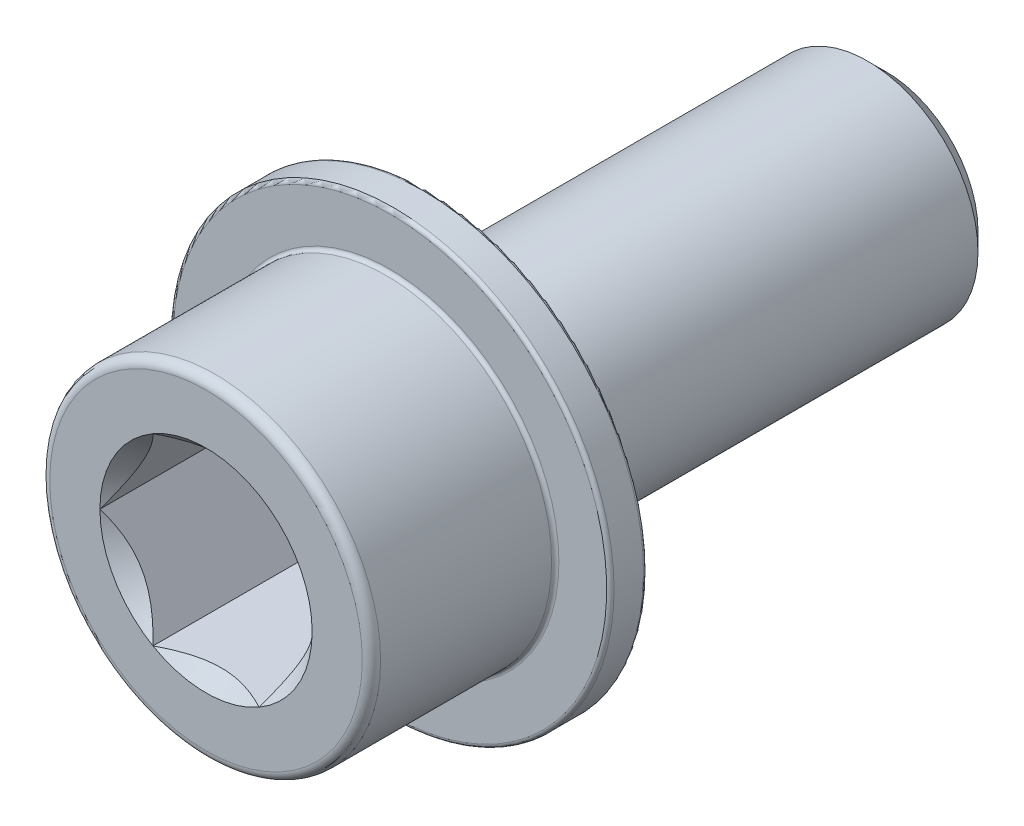
SolidWorks part; units mm, degrees
material "Acciaio inossidabile (ferroso)"
ref_plane "Piano frontale" through (0, 0, 0) normal (0, 0, 1) x (1, 0, 0)
ref_plane "Piano superiore" through (0, 0, 0) normal (0, 1, 0) x (1, 0, 0)
ref_plane "Piano destro" through (0, 0, 0) normal (1, 0, 0) x (0, 0, -1)
sketch "Schizzo1" plane through (0, 0, 0) normal (0, 0, 1) x (1, 0, 0)
  circle A0 centre (0, 0) radius 6
  dimension "D1" = 12
extrude "Estrusione-Estrusione1" add sketch "Schizzo1" along normal blind 25
cosmetic thread "Filettatura cosmetica2" parameters "D2"=10.072
chamfer "Smusso1" distance 1 angle 45 1 edges at (6, 0, 0)
sketch "Schizzo6" plane through (0, 0, 25) normal (0, 0, 1) x (1, 0, 0)
  circle A0 centre (0, 0) radius 9
  dimension "D1" = 18
extrude "Estrusione-Estrusione3" add sketch "Schizzo6" along normal blind 12
sketch "Schizzo7" plane through (0, 0, 37) normal (0, 0, 1) x (1, 0, 0)
  line L1 (2.8868, 5) -> (-2.8868, 5)
  line L2 (-2.8868, 5) -> (-5.7735, 0)
  line L3 (-5.7735, 0) -> (-2.8868, -5)
  line L4 (-2.8868, -5) -> (2.8868, -5)
  line L5 (2.8868, -5) -> (5.7735, 0)
  line L6 (5.7735, 0) -> (2.8868, 5)
  circle A1 centre (0, 0) radius 5 construction
  dimension "D1" = 10
extrude "Taglio-Estrusione3" cut sketch "Schizzo7" against normal blind 8
sketch "Schizzo8" plane through (0, 0, 37) normal (0, 0, 1) x (1, 0, 0)
  circle A0 centre (0, 0) radius 5.7735
extrude "Taglio-Estrusione4" cut sketch "Schizzo8" against normal blind 1 draft 43
fillet "Raccordo4" radius 0.5 1 edges at (9, 0, 37)
sketch "Schizzo9" plane through (0, 0, 25) normal (0, 0, -1) x (-1, 0, 0)
  circle A0 centre (0, 0) radius 9
  circle A1 centre (0, 0) radius 12
  dimension "D1" = 24
  dimension "D2" = 18
extrude "Estrusione-Estrusione4" add sketch "Schizzo9" against normal blind 2
fillet "Raccordo5" radius 0.2 3 edges at (-12, 0, 27) (-12, 0, 25) (-9, 0, 27)
